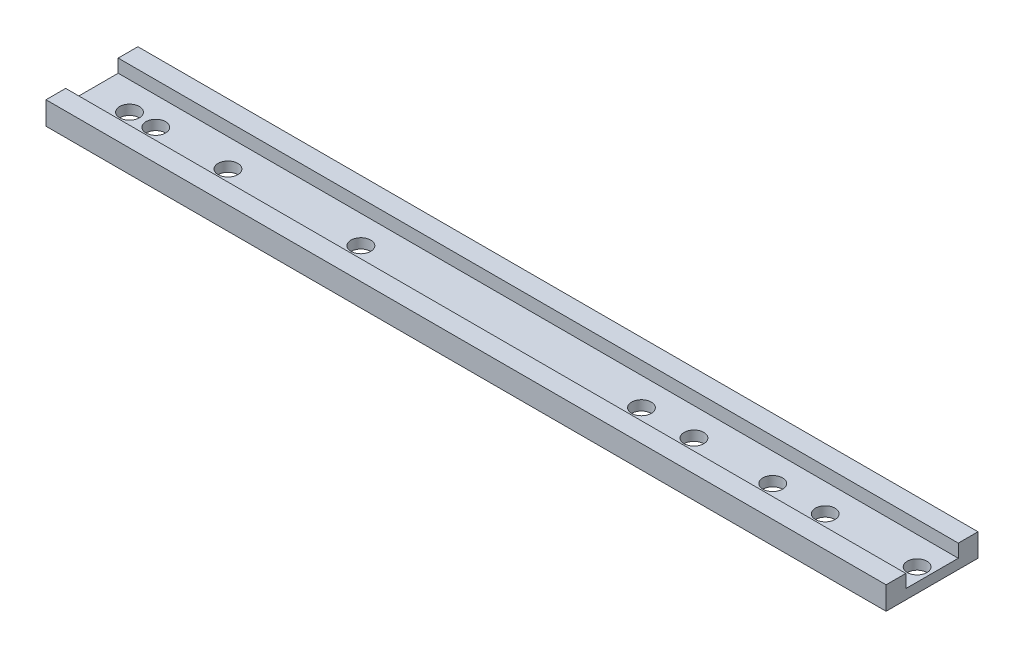
SolidWorks part; units mm, degrees
material "Chrome Stainless Steel"
ref_plane "Front Plane" through (0, 0, 0) normal (0, 0, 1) x (1, 0, 0)
ref_plane "Top Plane" through (0, 0, 0) normal (0, 1, 0) x (1, 0, 0)
ref_plane "Right Plane" through (0, 0, 0) normal (1, 0, 0) x (0, 0, -1)
sketch "Sketch1" plane through (0, 0, 0) normal (1, 0, 0) x (0, 0, -1)
  line L0 (0, 0.4375) -> (0, 0)
  line L1 (0, 0) -> (1.75, 0)
  line L2 (1.75, 0) -> (1.75, 0.4375)
  line L3 (1.75, 0.4375) -> (1.375, 0.4375)
  line L4 (1.375, 0.4375) -> (1.375, 0.1875)
  line L5 (1.375, 0.1875) -> (0.375, 0.1875)
  line L6 (0.375, 0.1875) -> (0.375, 0.4375)
  line L7 (0.375, 0.4375) -> (0, 0.4375)
  dimension "D1" = 0.4375
  dimension "D2" = 1.75
  dimension "D3" = 0.25
  dimension "D4" = 1
extrude "Boss-Extrude1" add sketch "Sketch1" along normal blind 16
scale "Scale1" scale about centroid uniform scaling yes scale factor 25.4
sketch "Sketch2" plane through (0, -4.2284, 0) normal (0, -1, 0) x (1, 0, 0)
  line L0 (-195.2, 0) -> (211.2, 0) construction
  line L1 (-195.2, 21.35) -> (-195.2, -23.1) construction
  line L2 (211.2, 21.35) -> (211.2, -23.1) construction
  circle A0 centre (-176.15, 0) radius 4.7625
  circle A1 centre (-163.45, 0) radius 4.7625
  circle A2 centre (-128.525, 0) radius 4.7625
  circle A3 centre (-64.2312, 0) radius 4.7625
  circle A4 centre (71.5, 0) radius 4.7625
  circle A5 centre (96.9, 0) radius 4.7625
  circle A6 centre (135, 0) radius 4.7625
  circle A7 centre (160.4, 0) radius 4.7625
  circle A8 centre (204.85, 0) radius 4.7625
  dimension "D10" = 9.525
  dimension "D1" = 19.05
  dimension "D2" = 31.75
  dimension "D3" = 66.675
  dimension "D4" = 130.9688
  dimension "D5" = 266.7
  dimension "D6" = 292.1
  dimension "D7" = 330.2
  dimension "D8" = 355.6
  dimension "D9" = 400.05
extrude "Cut-Extrude1" cut sketch "Sketch2" against normal through all
